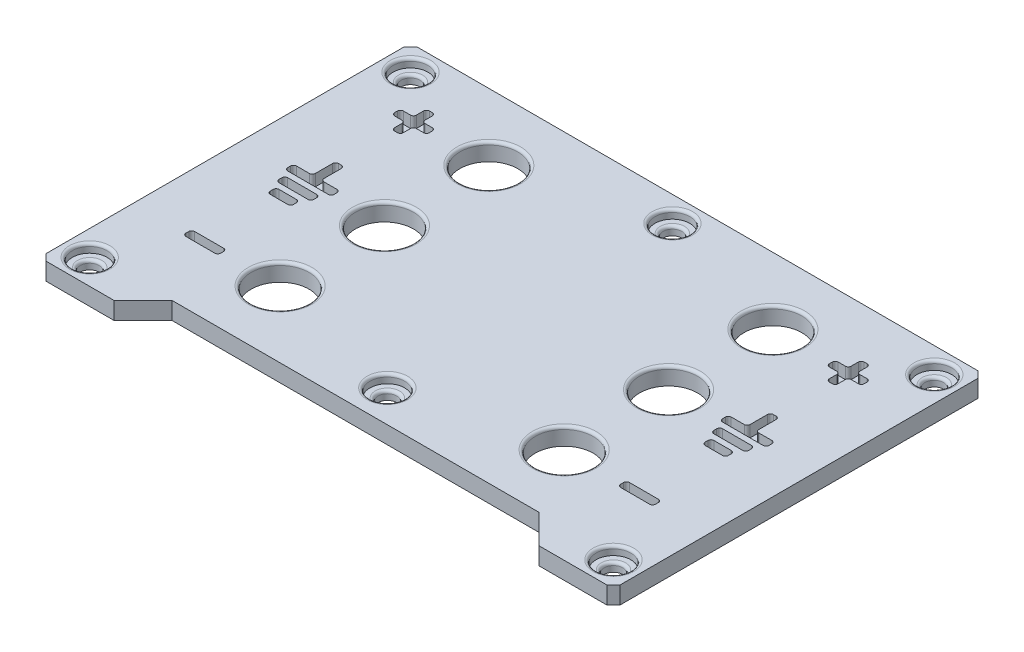
SolidWorks part; units mm, degrees
ref_plane "Front Plane" through (0, 0, 0) normal (0, 0, 1) x (1, 0, 0)
ref_plane "Top Plane" through (0, 0, 0) normal (0, 1, 0) x (1, 0, 0)
ref_plane "Right Plane" through (0, 0, 0) normal (1, 0, 0) x (0, 0, -1)
sketch "Sketch3" plane through (0, 0, 0) normal (0, 1, 0) x (1, 0, 0)
  line L0 (17.3523, -19.0435) -> (29.1096, -19.0435)
  line L5 (29.1096, -19.0435) -> (30.231, -17.9222)
  line L6 (30.231, -17.9222) -> (30.231, 43.8352)
  line L7 (30.231, 43.8352) -> (29.1096, 44.9565)
  line L8 (29.1096, 44.9565) -> (-67.6477, 44.9565)
  line L9 (-67.6477, 44.9565) -> (-68.769, 43.8352)
  line L10 (-68.769, 43.8352) -> (-68.769, -17.9222)
  line L11 (-68.769, -17.9222) -> (-67.6477, -19.0435)
  line L12 (-67.6477, -19.0435) -> (-55.8904, -19.0435)
  line L13 (-55.8904, -19.0435) -> (-50.8904, -14.0435)
  line L14 (-50.8904, -14.0435) -> (12.3523, -14.0435)
  line L15 (12.3523, -14.0435) -> (17.3523, -19.0435)
  line L16 (-19.269, 44.9565) -> (-19.269, -14.0435) construction
  line L17 (-68.769, 15.4565) -> (30.231, 15.4565) construction
  line L18 (-43.769, 44.9565) -> (-43.769, -14.0435) construction
  circle A0 centre (-64.439, 40.6265) radius 1.6
  circle A1 centre (-64.439, -14.7135) radius 1.6
  circle A2 centre (25.901, 40.6265) radius 1.6
  circle A3 centre (25.901, -14.7135) radius 1.6
  circle A4 centre (-43.769, 33.4565) radius 5
  circle A5 centre (-43.769, 15.4565) radius 5
  circle A6 centre (-43.769, -2.5435) radius 5
  circle A7 centre (5.231, -2.5435) radius 5
  circle A8 centre (5.231, 15.4565) radius 5
  circle A9 centre (5.231, 33.4565) radius 5
  circle A10 centre (-19.269, 40.6265) radius 1.6
  circle A11 centre (-19.269, -8.5435) radius 1.6
  point P22 (-19.269, 15.4565)
  point P26 (-19.269, 15.4565)
  point P28 (-43.769, 15.4565)
  point P46 (-19.269, 40.6265)
  point P47 (-19.269, -8.5435)
  dimension "D1" = 3.2
  dimension "D4" = 3.2
  dimension "D7" = 3.2
  dimension "D8" = 3.2
  dimension "D13" = 10
  dimension "D14" = 10
  dimension "D15" = 10
  dimension "D19" = 3.2
  dimension "D20" = 3.2
  dimension "D2" = 4.33
  dimension "D3" = 4.33
  dimension "D5" = 4.33
  dimension "D6" = 4.33
  dimension "D9" = 4.33
  dimension "D10" = 4.33
  dimension "D11" = 4.33
  dimension "D12" = 4.33
  dimension "D16" = 25
  dimension "D17" = 18
  dimension "D18" = 18
  dimension "D21" = 4.33
  dimension "D22" = 5.5
extrude "Boss-Extrude1" add sketch "Sketch3" against normal blind 3
sketch "Sketch4" plane through (0, 0, 0) normal (0, 1, 0) x (1, 0, 0)
  circle A0 centre (-64.439, 40.6265) radius 3
  circle A1 centre (-64.439, -14.7135) radius 3
  circle A2 centre (25.901, 40.6265) radius 3
  circle A3 centre (25.901, -14.7135) radius 3
  circle A4 centre (-19.269, 40.6265) radius 3
  circle A5 centre (-19.269, -8.5435) radius 3
  dimension "D1" = 6
  dimension "D2" = 6
  dimension "D3" = 6
  dimension "D4" = 6
  dimension "D5" = 6
  dimension "D6" = 6
extrude "Cut-Extrude1" cut sketch "Sketch4" against normal blind 1.5
fillet "Fillet1" radius 0.5 18 edges at (-64.439, -1.5, 16.3135) (-64.439, 0, 17.7135) (25.901, 0, 17.7135) (25.901, -1.5, 16.3135) (25.901, -1.5, -39.0265) (25.901, 0, -37.6265) (-64.439, -1.5, -39.0265) (-64.439, 0, -37.6265) (-19.269, -1.5, 10.1435) (-19.269, 0, 11.5435) (-19.269, -1.5, -39.0265) (-19.269, 0, -37.6265) (5.231, 0, -38.4565) (5.231, 0, -20.4565) (5.231, 0, -2.4565) (-43.769, 0, 7.5435) (-43.769, 0, -10.4565) (-43.769, 0, -28.4565)
sketch "Sketch5" plane through (0, 0, 0) normal (0, 1, 0) x (1, 0, 0)
  line L0 (-43.769, 33.4565) -> (-56.769, 33.4565) construction
  line L1 (-57.519, 30.4565) -> (-56.019, 30.4565)
  line L2 (-57.519, 30.4565) -> (-57.519, 32.7065)
  line L3 (-57.519, 36.4565) -> (-56.019, 36.4565)
  line L4 (-56.019, 30.4565) -> (-56.019, 32.7065)
  line L5 (-57.519, 30.4565) -> (-56.019, 36.4565) construction
  line L6 (-57.519, 36.4565) -> (-56.019, 30.4565) construction
  line L7 (-59.769, 32.7065) -> (-57.519, 32.7065)
  line L8 (-59.769, 32.7065) -> (-59.769, 34.2065)
  line L9 (-59.769, 34.2065) -> (-57.519, 34.2065)
  line L10 (-53.769, 32.7065) -> (-53.769, 34.2065)
  line L11 (-59.769, 32.7065) -> (-53.769, 34.2065) construction
  line L12 (-59.769, 34.2065) -> (-53.769, 32.7065) construction
  line L13 (-56.019, 34.2065) -> (-53.769, 34.2065)
  line L14 (-57.519, 34.2065) -> (-57.519, 36.4565)
  line L15 (-56.019, 32.7065) -> (-53.769, 32.7065)
  line L16 (-56.769, 33.4565) -> (-56.769, -2.5435) construction
  line L17 (-56.019, 34.2065) -> (-56.019, 36.4565)
  line L18 (-56.019, 16.7709) -> (-52.769, 16.7709)
  line L19 (-59.769, -3.2935) -> (-53.769, -3.2935)
  line L20 (-59.769, -3.2935) -> (-59.769, -1.7935)
  line L21 (-59.769, -1.7935) -> (-53.769, -1.7935)
  line L22 (-53.769, -3.2935) -> (-53.769, -1.7935)
  line L23 (-59.769, -3.2935) -> (-53.769, -1.7935) construction
  line L24 (-59.769, -1.7935) -> (-53.769, -3.2935) construction
  line L26 (-57.519, 16.7709) -> (-57.519, 20.7709)
  line L27 (-57.519, 20.7709) -> (-56.019, 20.7709)
  line L28 (-56.019, 16.7709) -> (-56.019, 20.7709)
  line L29 (-57.519, 16.7709) -> (-56.019, 20.7709) construction
  line L30 (-57.519, 20.7709) -> (-56.019, 16.7709) construction
  line L31 (-52.769, 16.7709) -> (-52.769, 15.2709)
  line L32 (-52.769, 15.2709) -> (-60.769, 15.2709)
  line L33 (-60.769, 15.2709) -> (-60.769, 16.7709)
  line L34 (-60.769, 16.7709) -> (-57.519, 16.7709)
  line L36 (-59.769, 12.7709) -> (-53.769, 12.7709)
  line L37 (-59.769, 12.7709) -> (-59.769, 14.2709)
  line L38 (-59.769, 14.2709) -> (-53.769, 14.2709)
  line L39 (-53.769, 12.7709) -> (-53.769, 14.2709)
  line L40 (-59.769, 12.7709) -> (-53.769, 14.2709) construction
  line L41 (-59.769, 14.2709) -> (-53.769, 12.7709) construction
  line L42 (-58.769, 10.2709) -> (-54.769, 10.2709)
  line L43 (-58.769, 10.2709) -> (-58.769, 11.7709)
  line L44 (-58.769, 11.7709) -> (-54.769, 11.7709)
  line L45 (-54.769, 10.2709) -> (-54.769, 11.7709)
  line L46 (-58.769, 10.2709) -> (-54.769, 11.7709) construction
  line L47 (-58.769, 11.7709) -> (-54.769, 10.2709) construction
  point P0 (-56.769, 33.4565)
  point P5 (-56.769, 33.4565)
  point P22 (-43.769, -2.5435)
  point P23 (-56.769, 18.7709)
  point P29 (-56.769, 15.2709)
  point P35 (-56.769, 11.0209)
  point P37 (-56.769, 13.5209)
  dimension "D1" = 6
  dimension "D2" = 1.5
  dimension "D3" = 10
  dimension "D4" = 1.5
  dimension "D5" = 6
  dimension "D6" = 1.5
  dimension "D7" = 8
  dimension "D8" = 1.5
  dimension "D9" = 4
  dimension "D10" = 1.5
  dimension "D11" = 6
  dimension "D12" = 1
  dimension "D13" = 1
  dimension "D14" = 1.5
  dimension "D15" = 4
  dimension "D16" = 6
sketch "Sketch6" plane through (0, 0, 0) normal (0, 1, 0) x (1, 0, 0)
  line L0 (29.1096, 44.9565) -> (-67.6477, 44.9565) construction
  line L1 (-50.8904, -14.0435) -> (12.3523, -14.0435) construction
  point P0 (-19.269, 44.9565)
  point P1 (-19.269, -14.0435)
ref_plane "Plane1" through (-19.269, 0, 0) normal (-1, 0, 0) x (0, 0, 1)
extrude "Cut-Extrude2" cut sketch "Sketch5" against normal blind 2
mirror "Mirror1" about plane through (-19.269, 0, 0) normal (-1, 0, 0) of "Cut-Extrude2"
fillet "Fillet2" radius 0.5 64 edges at (21.231, -1, 1.7935) (15.231, -1, 1.7935) (15.231, -1, 3.2935) (21.231, -1, 3.2935) (20.231, -1, -10.2709) (16.231, -1, -10.2709) (16.231, -1, -11.7709) (20.231, -1, -11.7709) (21.231, -1, -14.2709) (15.231, -1, -14.2709) (15.231, -1, -12.7709) (21.231, -1, -12.7709) (22.231, -1, -15.2709) (14.231, -1, -15.2709) (22.231, -1, -16.7709) (18.981, -1, -16.7709) (18.981, -1, -20.7709) (14.231, -1, -16.7709) (17.481, -1, -16.7709) (17.481, -1, -20.7709) (21.231, -1, -32.7065) (18.981, -1, -32.7065) (18.981, -1, -30.4565) (17.481, -1, -30.4565) (17.481, -1, -32.7065) (15.231, -1, -32.7065) (15.231, -1, -34.2065) (17.481, -1, -36.4565) (17.481, -1, -34.2065) (18.981, -1, -36.4565) (18.981, -1, -34.2065) (21.231, -1, -34.2065) (-53.769, -1, 1.7935) (-59.769, -1, 1.7935) (-59.769, -1, 3.2935) (-53.769, -1, 3.2935) (-54.769, -1, -10.2709) (-58.769, -1, -10.2709) (-58.769, -1, -11.7709) (-54.769, -1, -11.7709) (-53.769, -1, -14.2709) (-59.769, -1, -14.2709) (-59.769, -1, -12.7709) (-53.769, -1, -12.7709) (-52.769, -1, -15.2709) (-60.769, -1, -15.2709) (-60.769, -1, -16.7709) (-52.769, -1, -16.7709) (-56.019, -1, -16.7709) (-57.519, -1, -16.7709) (-56.019, -1, -20.7709) (-57.519, -1, -20.7709) (-53.769, -1, -32.7065) (-56.019, -1, -32.7065) (-56.019, -1, -30.4565) (-57.519, -1, -30.4565) (-57.519, -1, -32.7065) (-59.769, -1, -32.7065) (-59.769, -1, -34.2065) (-57.519, -1, -34.2065) (-56.019, -1, -34.2065) (-53.769, -1, -34.2065) (-57.519, -1, -36.4565) (-56.019, -1, -36.4565)
